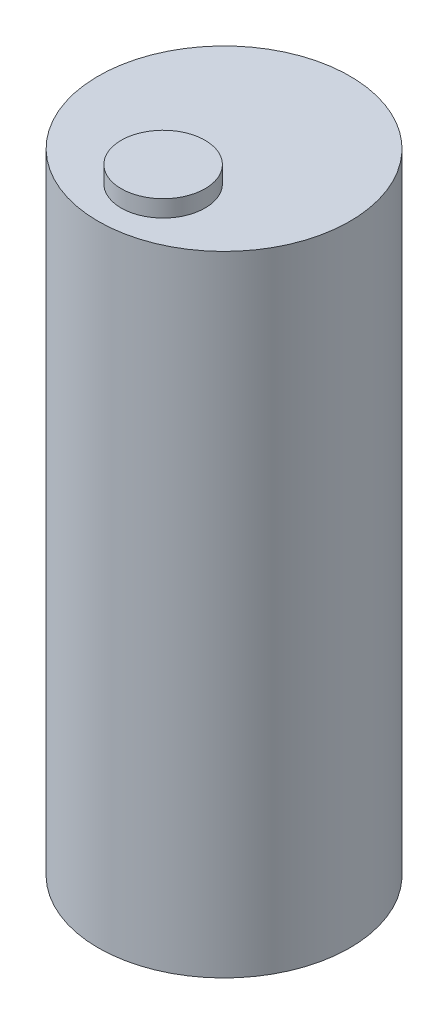
SolidWorks part; units mm, degrees
ref_plane "Front Plane" through (0, 0, 0) normal (0, 0, 1) x (1, 0, 0)
ref_plane "Top Plane" through (0, 0, 0) normal (0, 1, 0) x (1, 0, 0)
ref_plane "Right Plane" through (0, 0, 0) normal (1, 0, 0) x (0, 0, -1)
sketch "Sketch1" plane through (0, 0, 0) normal (0, 1, 0) x (1, 0, 0)
  circle A0 centre (0, 0) radius 15
  dimension "D1" = 30
extrude "Boss-Extrude1" add sketch "Sketch1" along normal blind 75
sketch "Sketch2" plane through (0, 75, 0) normal (0, 1, 0) x (1, 0, 0)
  line L0 (0, 0) -> (0, -7.2598) construction
  circle A0 centre (0, -7.2598) radius 5
  dimension "D1" = 10
extrude "Boss-Extrude2" add sketch "Sketch2" along normal blind 2
